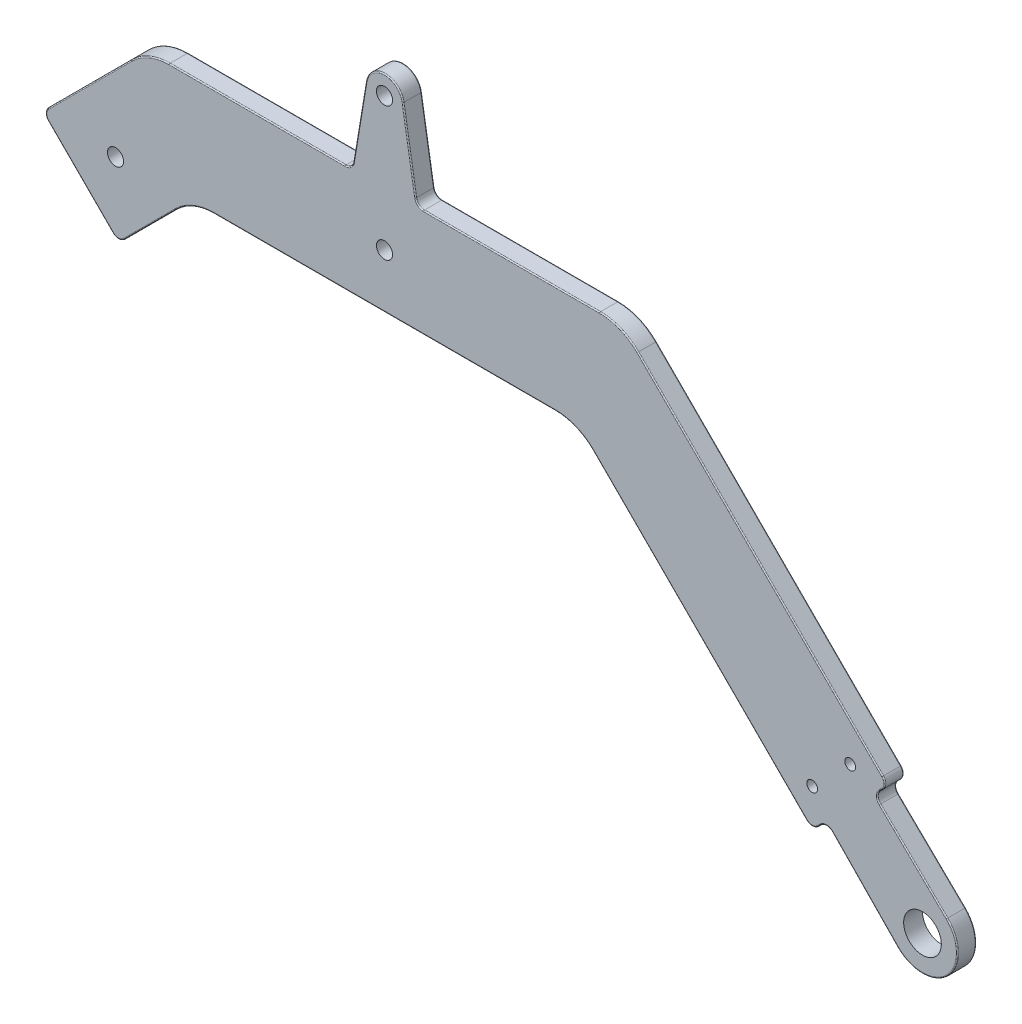
SolidWorks part; units mm, degrees
ref_plane "Front Plane" through (0, 0, 0) normal (0, 0, 1) x (1, 0, 0)
ref_plane "Top Plane" through (0, 0, 0) normal (0, 1, 0) x (1, 0, 0)
ref_plane "Right Plane" through (0, 0, 0) normal (1, 0, 0) x (0, 0, -1)
sketch "Sketch1" plane through (0, 0, 0) normal (0, 0, 1) x (1, 0, 0)
  line L0 (-100, 0) -> (100, 0) construction
  line L1 (-100, 0) -> (0, 100) construction
  line L2 (0, 100) -> (100, 0) construction
  line L3 (0, 0) -> (-50, 50) construction
  line L4 (-40, 60) -> (40, 60) construction
  line L5 (0, 100) -> (0, 60) construction
  circle A0 centre (-100, 0) radius 20
  circle A1 centre (0, 0) radius 20
  circle A2 centre (100, 0) radius 20
  dimension "D5" = 40
  dimension "D1" = 200
  dimension "D2" = 90
  dimension "D3" = 90
  dimension "D4" = 80
sketch "Sketch2" plane through (0, 0, 0) normal (0, 0, 1) x (1, 0, 0)
  line L0 (-56.5165, 43.4835) -> (-40, 60) construction
  line L1 (-100, 0) -> (0, 100) construction
  line L2 (-40, 60) -> (40, 60) construction
  line L3 (40, 60) -> (86.565, 13.435) construction
  line L4 (0, 100) -> (100, 0) construction
  line L5 (-49.4454, 36.4124) -> (-35.8579, 50)
  line L6 (-35.8579, 50) -> (35.8579, 50)
  line L7 (35.8579, 50) -> (79.4939, 6.364)
  line L8 (-63.5876, 50.5546) -> (-44.1421, 70)
  line L9 (-44.1421, 70) -> (44.1421, 70)
  line L10 (44.1421, 70) -> (93.636, 20.5061)
  line L11 (93.636, 20.5061) -> (79.4939, 6.364)
  line L12 (90.9809, 17.8509) -> (104.534, 4.6576)
  line L13 (82.1491, 9.0191) -> (95.3424, -4.534)
  line L14 (90.1005, 24.0416) -> (75.9584, 9.8995) construction
  line L15 (0, 100) -> (0, 60) construction
  line L16 (-6, 70) -> (-3.4532, 85.4203)
  line L17 (6, 70) -> (3.4532, 85.4203)
  line L18 (-63.5876, 50.5546) -> (-49.4454, 36.4124)
  circle A0 centre (100, 0) radius 10
  circle A1 centre (100, 0) radius 3.5
  arc A2 (95.3424, -4.534) -> (104.534, 4.6576) centre (100, 0) ccw
  circle A3 centre (100, 0) radius 20 construction
  circle A4 centre (79.4939, 13.435) radius 1
  circle A5 centre (100, 0) radius 6.5 construction
  circle A6 centre (86.565, 20.5061) radius 1
  circle A7 centre (0, 60) radius 1.5
  circle A8 centre (0, 84.85) radius 1.5
  arc A9 (3.4532, 85.4203) -> (-3.4532, 85.4203) centre (0, 84.85) ccw
  circle A10 centre (-50, 50) radius 1.5
  circle A11 centre (0, 84.85) radius 3.5 construction
  point P29 (106.5, 0)
  point P49 (3.5, 82)
  point P53 (0, 70)
  dimension "D4" = 20
  dimension "D5" = 7
  dimension "D9" = 2
  dimension "D12" = 3
  dimension "D17" = 3
  dimension "D3" = 27.5
  dimension "D7" = 19
  dimension "D8" = 5
  dimension "D10" = 5
  dimension "D11" = 5
  dimension "D13" = 14.85
  dimension "D15" = 6
  dimension "D16" = 6
  dimension "D1" = 10
  dimension "D2" = 10
  dimension "D6" = 3
  dimension "D14" = 2
sketch "Sketch3" plane through (0, 0, 0) normal (0, 0, 1) x (1, 0, 0)
  line L0 (-88.9571, 11.0429) -> (-50, 50)
  line L1 (-100, 0) -> (0, 100) construction
  line L2 (-50, 50) -> (-13.435, 13.435)
  line L3 (0, 0) -> (-50, 50) construction
  line L4 (-79.4939, 6.364) -> (-50, 35.8579)
  line L5 (-50, 35.8579) -> (-20.5061, 6.364)
  line L6 (-93.636, 20.5061) -> (-50, 64.1421)
  line L7 (-50, 64.1421) -> (-6.364, 20.5061)
  line L8 (-96.0281, 18.114) -> (-50, 64.1421) construction
  line L9 (-81.886, 3.9719) -> (-50, 35.8579) construction
  line L10 (-93.636, 20.5061) -> (-79.4939, 6.364)
  line L11 (-6.364, 20.5061) -> (-20.5061, 6.364)
  line L12 (-91.1612, 18.0312) -> (-104.5962, 4.5962)
  line L13 (-81.9688, 8.8388) -> (-95.4038, -4.5962)
  line L14 (-18.0312, 8.8388) -> (-4.5962, -4.5962)
  line L15 (-9.0191, 17.8509) -> (4.534, 4.6576)
  line L16 (-86.3104, 27.8317) -> (-72.1683, 13.6896) construction
  line L17 (-14.2627, 28.4049) -> (-28.4049, 14.2627) construction
  circle A0 centre (-100, 0) radius 10 construction
  circle A1 centre (-100, 0) radius 3.5
  circle A2 centre (0, 0) radius 10 construction
  circle A3 centre (0, 0) radius 3.5
  circle A4 centre (0, 0) radius 6.5
  circle A5 centre (-100, 0) radius 6.5
  circle A6 centre (0, 0) radius 20 construction
  circle A7 centre (-82.7749, 24.2962) radius 1
  circle A8 centre (-75.7038, 17.2251) radius 1
  circle A9 centre (-24.8693, 17.7983) radius 1
  circle A10 centre (-17.7983, 24.8693) radius 1
  circle A11 centre (-50, 50) radius 1.5 construction
  circle A12 centre (-50, 50) radius 1.5
  dimension "D1" = 20
  dimension "D2" = 7
  dimension "D11" = 2
  dimension "D7" = 19
  dimension "D8" = 19
  dimension "D9" = 5
  dimension "D10" = 5
  dimension "D12" = 5
  dimension "D13" = 5
  dimension "D3" = 3
  dimension "D4" = 3
  dimension "D5" = 10
  dimension "D6" = 10
sketch "Sketch4" plane through (0, 0, 0) normal (0, 0, 1) x (1, 0, 0)
  line L0 (-57.5, 93.3579) -> (57.5, 93.3579)
  line L1 (57.5, 93.3579) -> (57.5, 83.3579)
  line L2 (57.5, 83.3579) -> (44.1421, 70)
  line L3 (-44.1421, 70) -> (-57.5, 83.3579)
  line L4 (-57.5, 83.3579) -> (-57.5, 93.3579)
  line L5 (-44.1421, 70) -> (44.1421, 70) construction
  line L6 (4, 60) -> (4, 70)
  line L7 (-4, 60) -> (-4, 70)
  line L8 (-22.5, 84.85) -> (22.5, 84.85) construction
  line L9 (-22.5, 89.35) -> (22.5, 89.35)
  line L10 (-22.5, 80.35) -> (22.5, 80.35)
  line L11 (0, 100) -> (0, 60) construction
  circle A0 centre (0, 60) radius 1.5 construction
  circle A1 centre (0, 60) radius 1.5
  circle A2 centre (0, 60) radius 4
  arc A3 (-22.5, 89.35) -> (-22.5, 80.35) centre (-22.5, 84.85) ccw
  arc A4 (22.5, 80.35) -> (22.5, 89.35) centre (22.5, 84.85) ccw
  point P21 (0, 84.85)
  point P36 (0, 93.3579)
  point P39 (0, 80)
  dimension "D6" = 4.5
  dimension "D1" = 115
  dimension "D2" = 10
  dimension "D3" = 10
  dimension "D5" = 45
  dimension "D7" = 4.0079
  dimension "D4" = 2.5
sketch "Sketch5" plane through (0, 0, 0) normal (0, 0, 1) x (1, 0, 0)
  line L0 (90.9809, 17.8509) -> (104.534, 4.6576) construction
  line L1 (82.1491, 9.0191) -> (95.3424, -4.534) construction
  line L2 (-6, 70) -> (-3.4532, 85.4203) construction
  line L3 (6, 70) -> (3.4532, 85.4203) construction
  line L4 (90.9809, 17.8509) -> (104.534, 4.6576)
  line L5 (82.1491, 9.0191) -> (95.3424, -4.534)
  line L6 (-6, 70) -> (-3.4532, 85.4203)
  line L7 (6, 70) -> (3.4532, 85.4203)
  line L8 (-44.1421, 70) -> (-63.5876, 50.5546)
  line L9 (44.1421, 70) -> (-44.1421, 70)
  line L10 (93.636, 20.5061) -> (44.1421, 70)
  line L11 (79.4939, 6.364) -> (93.636, 20.5061)
  line L12 (35.8579, 50) -> (79.4939, 6.364)
  line L13 (-35.8579, 50) -> (35.8579, 50)
  line L14 (-49.4454, 36.4124) -> (-35.8579, 50)
  line L15 (-63.5876, 50.5546) -> (-49.4454, 36.4124)
  line L16 (-44.1421, 70) -> (-63.5876, 50.5546)
  line L17 (44.1421, 70) -> (6, 70)
  line L18 (93.636, 20.5061) -> (44.1421, 70)
  line L19 (79.4939, 6.364) -> (82.1491, 9.0191)
  line L20 (35.8579, 50) -> (79.4939, 6.364)
  line L21 (-35.8579, 50) -> (35.8579, 50)
  line L22 (-49.4454, 36.4124) -> (-35.8579, 50)
  line L23 (-63.5876, 50.5546) -> (-49.4454, 36.4124)
  line L24 (-6, 70) -> (-44.1421, 70)
  line L25 (90.9809, 17.8509) -> (93.636, 20.5061)
  arc A0 (95.3424, -4.534) -> (104.534, 4.6576) centre (100, 0) ccw construction
  circle A1 centre (100, 0) radius 3.5
  circle A2 centre (100, 0) radius 3.5
  circle A3 centre (100, 0) radius 10
  circle A4 centre (100, 0) radius 10
  circle A5 centre (0, 84.85) radius 1.5
  circle A6 centre (0, 84.85) radius 1.5
  circle A7 centre (0, 60) radius 1.5
  circle A8 centre (0, 60) radius 1.5
  circle A9 centre (86.565, 20.5061) radius 1
  circle A10 centre (86.565, 20.5061) radius 1
  circle A11 centre (79.4939, 13.435) radius 1
  circle A12 centre (79.4939, 13.435) radius 1
  circle A13 centre (-50, 50) radius 1.5
  circle A14 centre (-50, 50) radius 1.5
  arc A15 (3.4532, 85.4203) -> (-3.4532, 85.4203) centre (0, 84.85) ccw construction
  arc A16 (95.3424, -4.534) -> (104.534, 4.6576) centre (100, 0) ccw
  arc A17 (3.4532, 85.4203) -> (-3.4532, 85.4203) centre (0, 84.85) ccw
  dimension "D9" = 24.5153
  dimension "D10" = 24.5153
  dimension "D1" = 0
  dimension "D2" = 0
  dimension "D3" = 0
  dimension "D4" = 0
  dimension "D5" = 0
  dimension "D6" = 0
  dimension "D7" = 0
  dimension "D8" = 0
extrude "Boss-Extrude2" add sketch "Sketch5" along normal blind 3.5 contours L7 A17 L6 L24 L16 L23 L22 L21 L20 L19 L5 A4 L4 L25 L18 L17 A6 A8 A10 A12 A14 | L5 A16 L4 A4 A2
fillet "Fillet1" radius 10 4 edges at (44.1421, 70, 1.75) (35.8579, 50, 1.75) (-35.8579, 50, 1.75) (-44.1421, 70, 1.75)
fillet "Fillet2" radius 1.5 8 edges at (-49.4454, 36.4124, 1.75) (-63.5876, 50.5546, 1.75) (6, 70, 1.75) (-6, 70, 1.75) (90.9809, 17.8509, 1.75) (93.636, 20.5061, 1.75) (82.1491, 9.0191, 1.75) (79.4939, 6.364, 1.75)
fillet "Fillet3" radius 0.2 56 edges at (43.8268, 69.2388, 3.5) (69.8232, 44.3189, 3.5) (93.0147, 20.5061, 3.5) (92.3156, 19.1857, 3.5) (91.6166, 17.8552, 3.5) (98.3021, 10.724, 3.5) (104.5962, -4.5962, 3.5) (89.276, 1.6979, 3.5) (82.1448, 8.3834, 3.5) (80.8143, 7.6844, 3.5) (79.4939, 6.9853, 3.5) (58.61, 27.2478, 3.5) (35.5426, 49.2388, 3.5) (0, 50, 3.5) (-35.5426, 49.2388, 3.5) (-43.5858, 42.2721, 3.5) (-49.4454, 37.0337, 3.5) (-56.5165, 43.4835, 3.5) (-62.9663, 50.5546, 3.5) (-54.799, 59.3431, 3.5) (-43.8268, 69.2388, 3.5) (-23.6363, 70, 3.5) (-6.3022, 70.3562, 3.5) (-4.6229, 78.3379, 3.5) (0, 88.35, 3.5) (4.6229, 78.3379, 3.5) (6.3022, 70.3562, 3.5) (43.8268, 69.2388, 0) (69.8232, 44.3189, 0) (93.0147, 20.5061, 0) (92.3156, 19.1857, 0) (91.6166, 17.8552, 0) (98.3021, 10.724, 0) (104.5962, -4.5962, 0) (89.276, 1.6979, 0) (82.1448, 8.3834, 0) (80.8143, 7.6844, 0) (79.4939, 6.9853, 0) (58.61, 27.2478, 0) (35.5426, 49.2388, 0) (0, 50, 0) (-35.5426, 49.2388, 0) (-43.5858, 42.2721, 0) (-49.4454, 37.0337, 0) (-56.5165, 43.4835, 0) (-62.9663, 50.5546, 0) (-54.799, 59.3431, 0) (-43.8268, 69.2388, 0) (-23.6363, 70, 0) (-6.3022, 70.3562, 0) (-4.6229, 78.3379, 0) (0, 88.35, 0) (4.6229, 78.3379, 0) (6.3022, 70.3562, 0) (23.6363, 70, 3.5) (23.6363, 70, 0)
